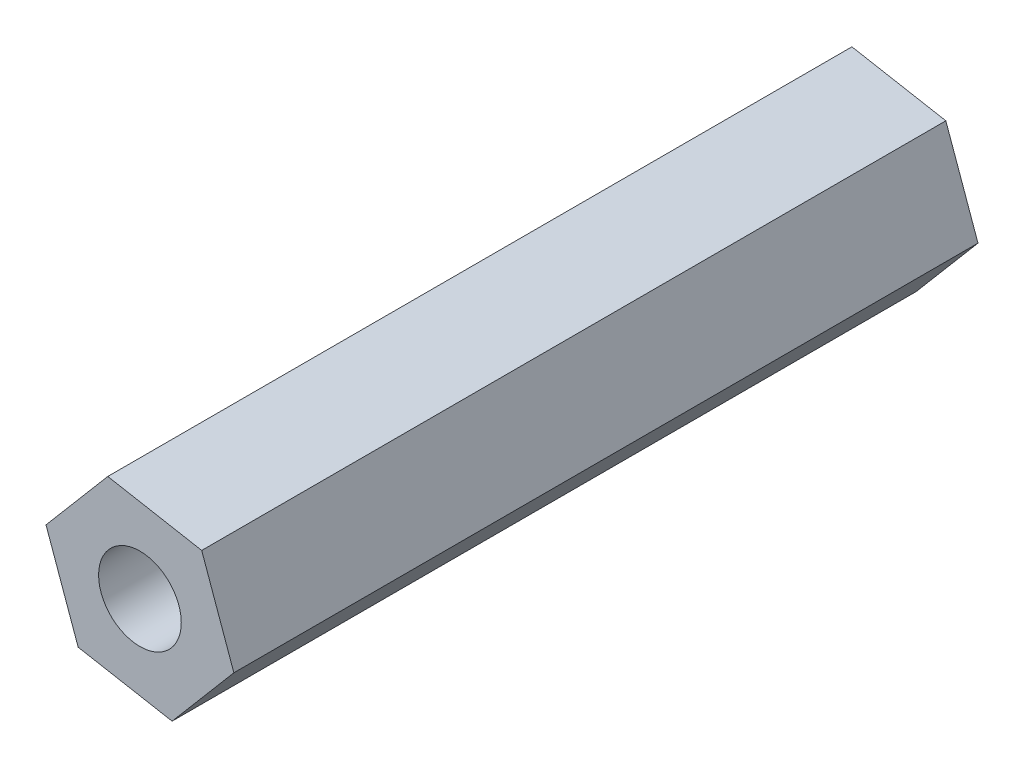
SolidWorks part; units mm, degrees
material "ABS"
ref_plane "Plano frontal" through (0, 0, 0) normal (0, 0, 1) x (1, 0, 0)
ref_plane "Plano superior" through (0, 0, 0) normal (0, 1, 0) x (1, 0, 0)
ref_plane "Plano direito" through (0, 0, 0) normal (1, 0, 0) x (0, 0, -1)
sketch "Esboço1" plane through (0, 0, 0) normal (0, 0, 1) x (1, 0, 0)
  line L1 (12.9332, -4.1439) -> (9.5251, -3.5237)
  line L2 (9.5251, -3.5237) -> (7.2839, -6.1651)
  line L3 (7.2839, -6.1651) -> (8.4508, -9.4267)
  line L4 (8.4508, -9.4267) -> (11.8589, -10.0469)
  line L5 (11.8589, -10.0469) -> (14.1001, -7.4055)
  line L6 (14.1001, -7.4055) -> (12.9332, -4.1439)
  circle A0 centre (10.692, -6.7853) radius 3 construction
extrude "Ressalto-extrusão1" add sketch "Esboço1" along normal blind 27
sketch "Esboço4" plane through (0, 0, 0) normal (0, 0, -1) x (-1, 0, 0)
  line L1 (-12.9332, -4.1439) -> (-9.5251, -3.5237) construction
  circle A0 centre (-10.692, -6.7853) radius 1.5
  dimension "D1" = 3
extrude "Corte-extrusão2" cut sketch "Esboço4" against normal blind 40
